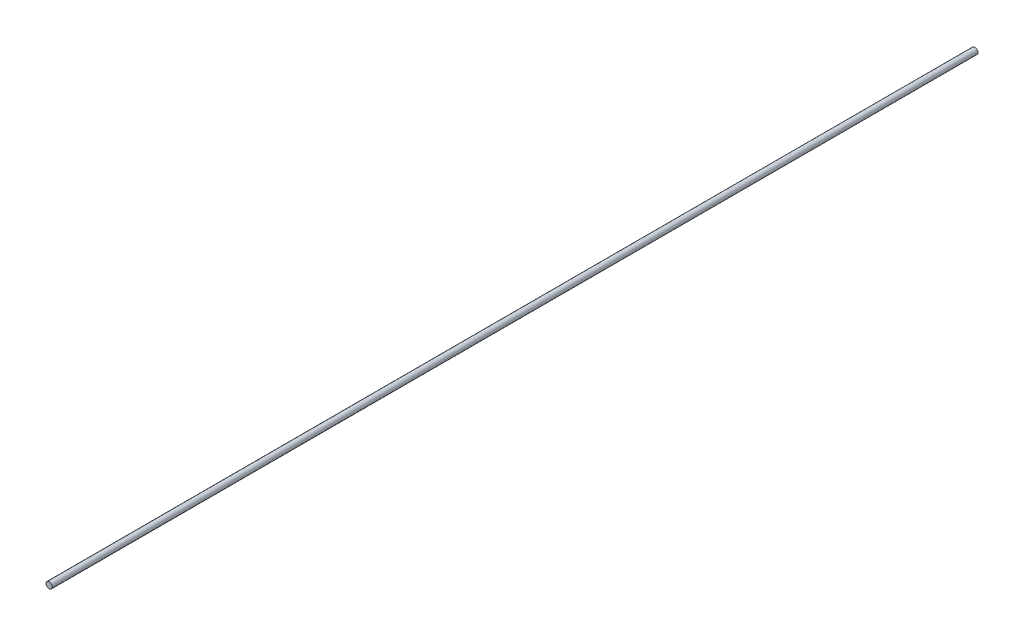
SolidWorks part; units mm, degrees
ref_plane "Front Plane" through (0, 0, 0) normal (0, 0, 1) x (1, 0, 0)
ref_plane "Top Plane" through (0, 0, 0) normal (0, 1, 0) x (1, 0, 0)
ref_plane "Right Plane" through (0, 0, 0) normal (1, 0, 0) x (0, 0, -1)
sketch "Sketch1" plane through (0, 0, 0) normal (0, 0, 1) x (1, 0, 0)
  circle A0 centre (0, 0) radius 2
extrude "Boss-Extrude1" add sketch "Sketch1" along normal blind 600
